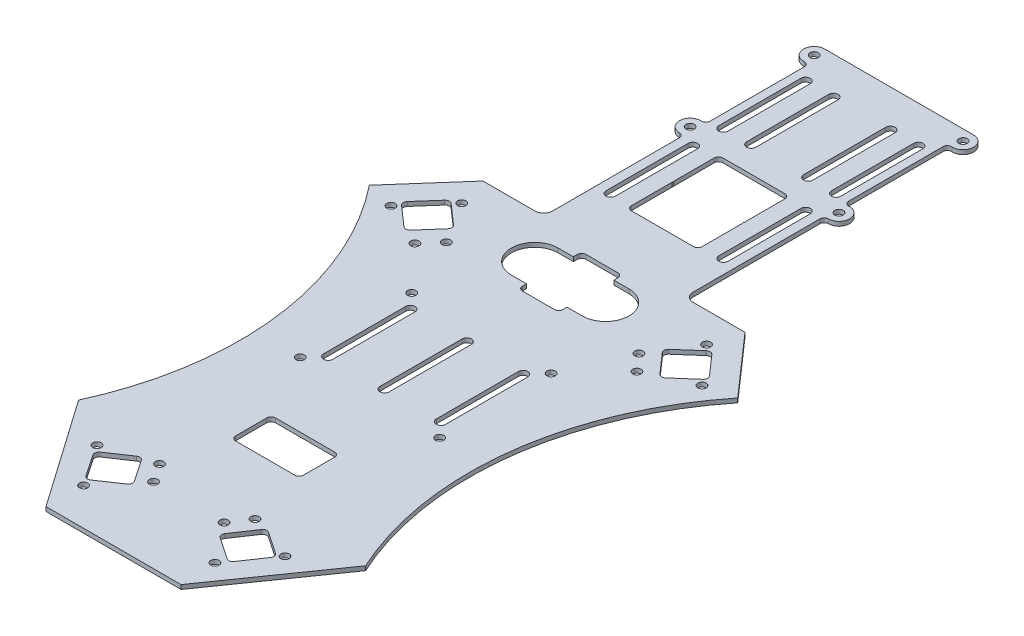
SolidWorks part; units mm, degrees
ref_plane "Front Plane" through (0, 0, 0) normal (0, 0, 1) x (1, 0, 0)
ref_plane "Top Plane" through (0, 0, 0) normal (0, 1, 0) x (1, 0, 0)
ref_plane "Right Plane" through (0, 0, 0) normal (1, 0, 0) x (0, 0, -1)
sketch "Sketch1" plane through (0, 0, 0) normal (0, 1, 0) x (1, 0, 0)
  line L0 (0, -163.8605) -> (0, 187.1526) construction
  line L1 (24.225, -100.314) -> (-24.225, -100.314)
  line L2 (-47, 79.196) -> (-66.075, 57.4987)
  line L3 (-51.475, -61.3813) -> (-24.225, -100.314)
  line L4 (-47, 79.196) -> (-28.38, 79.196)
  line L5 (-25.2, 82.376) -> (-25.2, 127.896)
  line L6 (26.7, 181.496) -> (-26.7, 181.496)
  line L7 (-24.85, 172.4076) -> (-24.85, 138.4845)
  line L8 (-20.22, 168.1277) -> (-20.22, 138.6677) construction
  line L9 (-18.54, 168.1277) -> (-18.54, 138.6677)
  line L10 (-21.9, 168.1277) -> (-21.9, 138.6677)
  line L11 (-10.22, 168.1277) -> (-10.22, 138.6677) construction
  line L12 (-8.54, 168.1277) -> (-8.54, 138.6677)
  line L13 (-11.9, 168.1277) -> (-11.9, 138.6677)
  line L14 (-20.22, 127.716) -> (-20.22, 98.256) construction
  line L15 (-18.54, 127.716) -> (-18.54, 98.256)
  line L16 (-21.9, 127.716) -> (-21.9, 98.256)
  line L17 (-20.22, 26.376) -> (-20.22, -3.084) construction
  line L18 (-18.54, 26.376) -> (-18.54, -3.084)
  line L19 (-21.9, 26.376) -> (-21.9, -3.084)
  line L20 (0, 26.376) -> (0, -3.084) construction
  line L21 (1.68, 26.376) -> (1.68, -3.084)
  line L22 (-1.68, 26.376) -> (-1.68, -3.084)
  line L23 (-54.1827, 59.2578) -> (-47.9366, 66.3626)
  line L24 (11.13, 129.396) -> (-11.13, 129.396)
  line L25 (12.7, 127.826) -> (12.7, 113.506)
  line L26 (11.13, 111.936) -> (-11.13, 111.936)
  line L27 (-12.7, 127.826) -> (-12.7, 113.506)
  line L28 (12.7, 129.396) -> (-12.7, 111.936) construction
  line L29 (12.7, 111.936) -> (-12.7, 129.396) construction
  line L30 (11.13, 114.036) -> (-11.13, 114.036)
  line L31 (12.7, 112.466) -> (12.7, 98.146)
  line L32 (11.13, 96.576) -> (-11.13, 96.576)
  line L33 (-12.7, 112.466) -> (-12.7, 98.146)
  line L34 (12.7, 114.036) -> (-12.7, 96.576) construction
  line L35 (12.7, 96.576) -> (-12.7, 114.036) construction
  line L36 (-54.0402, 57.0421) -> (-46.9354, 50.796)
  line L37 (-45.7209, 66.5051) -> (-38.6161, 60.2591)
  line L38 (-44.7197, 50.9385) -> (-38.4736, 58.0433)
  line L39 (-31.8561, -75.8408) -> (-26.6116, -83.5936)
  line L40 (-12.7, 71.876) -> (-7.265, 71.876)
  line L41 (-12.7, 55.076) -> (-7.265, 55.076)
  line L42 (7.265, 71.876) -> (12.7, 71.876)
  line L43 (5.695, 74.876) -> (-5.695, 74.876)
  line L44 (7.265, 73.306) -> (7.265, 71.876)
  line L45 (5.695, 52.076) -> (-5.695, 52.076)
  line L46 (-7.265, 73.306) -> (-7.265, 71.876)
  line L47 (7.265, 74.876) -> (6.9033, 74.3085) construction
  line L48 (7.265, 52.076) -> (6.9033, 52.6436) construction
  line L49 (7.265, 55.076) -> (7.265, 53.646)
  line L50 (-7.265, 55.076) -> (-7.265, 53.646)
  line L51 (-6.9033, 52.6436) -> (-7.265, 52.076) construction
  line L52 (7.265, 55.076) -> (12.7, 55.076)
  line L53 (-6.9033, 74.3085) -> (-7.265, 74.876) construction
  line L54 (-31.4354, -73.6607) -> (-23.6827, -68.4162)
  line L55 (-24.4315, -84.0143) -> (-16.6788, -78.7698)
  line L56 (-21.5026, -68.837) -> (-16.2581, -76.5897)
  line L57 (24.4315, -84.0143) -> (16.6788, -78.7698)
  line L58 (10.615, -31.604) -> (-10.615, -31.604)
  line L59 (12.185, -33.174) -> (12.185, -44.354)
  line L60 (10.615, -45.924) -> (-10.615, -45.924)
  line L61 (-12.185, -33.174) -> (-12.185, -44.354)
  line L62 (12.185, -31.604) -> (-12.185, -45.924) construction
  line L63 (12.185, -45.924) -> (-12.185, -31.604) construction
  line L64 (21.5026, -68.837) -> (16.2581, -76.5897)
  line L65 (31.4354, -73.6607) -> (23.6827, -68.4162)
  line L66 (31.8561, -75.8408) -> (26.6116, -83.5936)
  line L67 (51.475, -61.3813) -> (24.225, -100.314)
  line L68 (20.22, 26.376) -> (20.22, -3.084) construction
  line L69 (18.54, 26.376) -> (18.54, -3.084)
  line L70 (21.9, 26.376) -> (21.9, -3.084)
  line L71 (54.0402, 57.0421) -> (46.9354, 50.796)
  line L72 (44.7197, 50.9385) -> (38.4736, 58.0433)
  line L73 (45.7209, 66.5051) -> (38.6161, 60.2591)
  line L74 (54.1827, 59.2578) -> (47.9366, 66.3626)
  line L75 (47, 79.196) -> (66.075, 57.4987)
  line L76 (47, 79.196) -> (28.38, 79.196)
  line L77 (20.22, 127.716) -> (20.22, 98.256) construction
  line L78 (18.54, 127.716) -> (18.54, 98.256)
  line L79 (21.9, 127.716) -> (21.9, 98.256)
  line L80 (10.22, 168.1277) -> (10.22, 138.6677) construction
  line L81 (8.54, 168.1277) -> (8.54, 138.6677)
  line L82 (11.9, 168.1277) -> (11.9, 138.6677)
  line L83 (20.22, 168.1277) -> (20.22, 138.6677) construction
  line L84 (18.54, 168.1277) -> (18.54, 138.6677)
  line L85 (21.9, 168.1277) -> (21.9, 138.6677)
  line L86 (25.2, 82.376) -> (25.2, 127.896)
  line L87 (24.85, 172.4076) -> (24.85, 138.4845)
  arc A0 (-51.475, -61.3813) -> (-66.075, 57.4987) centre (-155.1713, -13.7801) ccw
  arc A1 (-26.7, 181.496) -> (-26.4491, 173.9043) centre (-26.7, 177.696) ccw
  arc A2 (-26.4491, 136.9877) -> (-26.7, 129.396) centre (-26.7, 133.196) ccw
  arc A3 (-25.2, 127.896) -> (-26.7, 129.396) centre (-26.7, 127.896) ccw
  arc A4 (-24.85, 138.4845) -> (-26.4491, 136.9877) centre (-26.35, 138.4845) cw
  arc A5 (-24.85, 172.4076) -> (-26.4491, 173.9043) centre (-26.35, 172.4076) ccw
  arc A6 (-25.2, 82.376) -> (-28.38, 79.196) centre (-28.38, 82.376) cw
  arc A7 (-18.54, 168.1277) -> (-21.9, 168.1277) centre (-20.22, 168.1277) ccw
  arc A8 (-21.9, 138.6677) -> (-18.54, 138.6677) centre (-20.22, 138.6677) ccw
  arc A9 (-8.54, 168.1277) -> (-11.9, 168.1277) centre (-10.22, 168.1277) ccw
  arc A10 (-11.9, 138.6677) -> (-8.54, 138.6677) centre (-10.22, 138.6677) ccw
  arc A11 (-18.54, 127.716) -> (-21.9, 127.716) centre (-20.22, 127.716) ccw
  arc A12 (-21.9, 98.256) -> (-18.54, 98.256) centre (-20.22, 98.256) ccw
  arc A13 (-18.54, 26.376) -> (-21.9, 26.376) centre (-20.22, 26.376) ccw
  arc A14 (-21.9, -3.084) -> (-18.54, -3.084) centre (-20.22, -3.084) ccw
  arc A15 (1.68, 26.376) -> (-1.68, 26.376) centre (0, 26.376) ccw
  arc A16 (-1.68, -3.084) -> (1.68, -3.084) centre (0, -3.084) ccw
  arc A17 (11.13, 96.576) -> (12.7, 98.146) centre (11.13, 98.146) ccw
  arc A18 (12.7, 112.466) -> (11.13, 114.036) centre (11.13, 112.466) ccw
  arc A19 (-12.7, 112.466) -> (-11.13, 114.036) centre (-11.13, 112.466) cw
  arc A20 (-11.13, 96.576) -> (-12.7, 98.146) centre (-11.13, 98.146) cw
  arc A21 (12.7, 113.506) -> (11.13, 111.936) centre (11.13, 113.506) cw
  arc A22 (-11.13, 111.936) -> (-12.7, 113.506) centre (-11.13, 113.506) cw
  arc A23 (-11.13, 129.396) -> (-12.7, 127.826) centre (-11.13, 127.826) ccw
  arc A24 (12.7, 127.826) -> (11.13, 129.396) centre (11.13, 127.826) ccw
  arc A25 (-46.9354, 50.796) -> (-44.7197, 50.9385) centre (-45.8988, 51.9751) ccw
  arc A26 (-54.0402, 57.0421) -> (-54.1827, 59.2578) centre (-53.0036, 58.2212) cw
  arc A27 (-38.4736, 58.0433) -> (-38.6161, 60.2591) centre (-39.6527, 59.0799) ccw
  arc A28 (-45.7209, 66.5051) -> (-47.9366, 66.3626) centre (-46.7575, 65.326) ccw
  arc A29 (-12.7, 71.876) -> (-12.7, 55.076) centre (-12.7, 63.476) ccw
  arc A30 (12.7, 55.076) -> (12.7, 71.876) centre (12.7, 63.476) ccw
  arc A31 (7.265, 53.646) -> (5.695, 52.076) centre (5.695, 53.646) cw
  arc A32 (7.265, 73.306) -> (5.695, 74.876) centre (5.695, 73.306) ccw
  arc A33 (-5.695, 74.876) -> (-7.265, 73.306) centre (-5.695, 73.306) ccw
  arc A34 (-7.265, 53.646) -> (-5.695, 52.076) centre (-5.695, 53.646) ccw
  arc A35 (-26.6116, -83.5936) -> (-24.4315, -84.0143) centre (-25.3112, -82.7139) ccw
  arc A36 (-16.6788, -78.7698) -> (-16.2581, -76.5897) centre (-17.5585, -77.4694) ccw
  arc A37 (-21.5026, -68.837) -> (-23.6827, -68.4162) centre (-22.803, -69.7166) ccw
  arc A38 (-31.8561, -75.8408) -> (-31.4354, -73.6607) centre (-30.5557, -74.9611) cw
  arc A39 (-12.185, -33.174) -> (-10.615, -31.604) centre (-10.615, -33.174) cw
  arc A40 (10.615, -31.604) -> (12.185, -33.174) centre (10.615, -33.174) cw
  arc A41 (12.185, -44.354) -> (10.615, -45.924) centre (10.615, -44.354) cw
  arc A42 (-10.615, -45.924) -> (-12.185, -44.354) centre (-10.615, -44.354) cw
  arc A43 (21.5026, -68.837) -> (23.6827, -68.4162) centre (22.803, -69.7166) cw
  arc A44 (46.9354, 50.796) -> (44.7197, 50.9385) centre (45.8988, 51.9751) cw
  arc A45 (45.7209, 66.5051) -> (47.9366, 66.3626) centre (46.7575, 65.326) cw
  arc A46 (54.0402, 57.0421) -> (54.1827, 59.2578) centre (53.0036, 58.2212) ccw
  arc A47 (38.4736, 58.0433) -> (38.6161, 60.2591) centre (39.6527, 59.0799) cw
  arc A48 (16.6788, -78.7698) -> (16.2581, -76.5897) centre (17.5585, -77.4694) cw
  arc A49 (26.6116, -83.5936) -> (24.4315, -84.0143) centre (25.3112, -82.7139) cw
  arc A50 (31.8561, -75.8408) -> (31.4354, -73.6607) centre (30.5557, -74.9611) ccw
  arc A51 (18.54, 26.376) -> (21.9, 26.376) centre (20.22, 26.376) cw
  arc A52 (21.9, -3.084) -> (18.54, -3.084) centre (20.22, -3.084) cw
  arc A53 (51.475, -61.3813) -> (66.075, 57.4987) centre (155.1713, -13.7801) cw
  arc A54 (25.2, 82.376) -> (28.38, 79.196) centre (28.38, 82.376) ccw
  arc A55 (18.54, 127.716) -> (21.9, 127.716) centre (20.22, 127.716) cw
  arc A56 (21.9, 98.256) -> (18.54, 98.256) centre (20.22, 98.256) cw
  arc A57 (8.54, 168.1277) -> (11.9, 168.1277) centre (10.22, 168.1277) cw
  arc A58 (11.9, 138.6677) -> (8.54, 138.6677) centre (10.22, 138.6677) cw
  arc A59 (18.54, 168.1277) -> (21.9, 168.1277) centre (20.22, 168.1277) cw
  arc A60 (21.9, 138.6677) -> (18.54, 138.6677) centre (20.22, 138.6677) cw
  arc A61 (25.2, 127.896) -> (26.7, 129.396) centre (26.7, 127.896) cw
  arc A62 (26.4491, 136.9877) -> (26.7, 129.396) centre (26.7, 133.196) cw
  arc A63 (24.85, 138.4845) -> (26.4491, 136.9877) centre (26.35, 138.4845) ccw
  arc A64 (24.85, 172.4076) -> (26.4491, 173.9043) centre (26.35, 172.4076) cw
  arc A65 (26.7, 181.496) -> (26.4491, 173.9043) centre (26.7, 177.696) cw
  point P23 (-24.85, 174.3768)
  point P26 (-25.2, 79.196)
  point P29 (-20.22, 153.3977)
  point P34 (-10.22, 153.3977)
  point P41 (-20.22, 136.9877)
  point P42 (0, 105.306)
  point P45 (-20.22, 112.986)
  point P50 (-20.22, 96.576)
  point P53 (-20.22, 129.396)
  point P58 (-20.22, 11.646)
  point P68 (0, 11.646)
  point P76 (-51.0597, 62.8102)
  point P77 (0, 120.666)
  point P118 (-46.9, 67.5418)
  point P121 (0, 63.476)
  point P126 (0, 63.476)
  point P149 (-29.2339, -79.7172)
  point P154 (-37.85, -80.8477)
  point P157 (-25.7319, -84.894)
  point P166 (0, -38.764)
  point P202 (0, -100.314)
  point P205 (20.22, 11.646)
  point P218 (20.22, 112.986)
  point P225 (10.22, 153.3977)
  point P232 (20.22, 153.3977)
  point P249 (0, 181.496)
  dimension "D1" = 48.45
  dimension "D4" = 114.1
  dimension "D8" = 7.6
  dimension "D9" = 7.6
  dimension "D11" = 49.7
  dimension "D16" = 1.5
  dimension "D17" = 3.18
  dimension "D18" = 1.68
  dimension "D25" = 1.57
  dimension "D29" = 1.57
  dimension "D30" = 8.4
  dimension "D34" = 1.57
  dimension "D35" = 1.57
  dimension "D40" = 1.57
  dimension "D45" = 1.57
  dimension "D2" = 27.25
  dimension "D3" = 14.6
  dimension "D5" = 118.88
  dimension "D6" = 28.89
  dimension "D7" = 21.8
  dimension "D10" = 26.7
  dimension "D12" = 44.5
  dimension "D13" = 6.31
  dimension "D14" = 102.3
  dimension "D15" = 281.81
  dimension "D19" = 29.46
  dimension "D20" = 10
  dimension "D21" = 20.22
  dimension "D22" = 155.12
  dimension "D23" = 25.4
  dimension "D24" = 12.5
  dimension "D26" = 12.6
  dimension "D27" = 7.77
  dimension "D28" = 21.7
  dimension "D31" = 7.32
  dimension "D32" = 14.53
  dimension "D33" = 22.8
  dimension "D36" = 12.5
  dimension "D37" = 12.5
  dimension "D38" = 7.77
  dimension "D39" = 15.42
  dimension "D41" = 7.77
  dimension "D42" = 24.37
  dimension "D43" = 14.32
  dimension "D44" = 213.1
  dimension "D46" = 14.32
extrude "Boss-Extrude1" add sketch "Sketch1" along normal blind 1.53 contours A65 L6 A1 A5 L7 A4 A2 A3 L5 A6 L4 L2 A0 L3 L1 L67 A53 L75 L76 A54 L86 A61 A62 A63 L87 A64 A50 L66 A49 L57 A48 L64 A43 L65 A34 L50 L41 A29 L40 L46 A33 L43 A32 L44 L42 A30 L52 L49 A31
sketch "Sketch2" plane through (0, 1.53, 0) normal (0, 1, 0) x (1, 0, 0)
  line L0 (-55.7847, 54.9808) -> (-43.9, 68.4994) construction
  line L1 (-51.0597, 62.8102) -> (-54.8635, 66.1543) construction
  line L2 (-54.1827, 59.2578) -> (-47.9366, 66.3626) construction
  line L3 (-39.8204, 47.6034) -> (-34.5383, 53.6116) construction
  line L4 (-41.5966, 54.4909) -> (-39.1657, 52.3538) construction
  line L5 (-44.7197, 50.9385) -> (-38.4736, 58.0433) construction
  line L6 (-25.005, 31.646) -> (-25.005, -8.354) construction
  line L7 (-21.9, 26.376) -> (-21.9, -3.084) construction
  line L8 (-12.185, -33.174) -> (-12.185, -44.354) construction
  line L9 (-21.9, 11.646) -> (-28.11, 11.646) construction
  line L10 (0, -116.2483) -> (0, 110.631) construction
  line L11 (-17.1237, -66.6957) -> (-12.6412, -73.322) construction
  line L12 (-29.2339, -79.7172) -> (-28.8942, -79.4874) construction
  line L13 (-31.8561, -75.8408) -> (-26.6116, -83.5936) construction
  line L14 (-18.8803, -72.7133) -> (-9.207, -66.1696) construction
  line L15 (-21.5026, -68.837) -> (-16.2581, -76.5897) construction
  line L16 (-51.475, -61.3813) -> (-24.225, -100.314) construction
  line L17 (-34.1468, -72.0886) -> (-24.0612, -86.9977) construction
  circle A0 centre (-26.7, 177.696) radius 1.5
  circle A1 centre (26.7, 177.696) radius 1.5
  circle A2 centre (-26.7, 133.196) radius 1.5
  circle A3 centre (26.7, 133.196) radius 1.5
  arc A4 (-26.7, 181.496) -> (-26.4491, 173.9043) centre (-26.7, 177.696) ccw construction
  arc A5 (26.4491, 173.9043) -> (26.7, 181.496) centre (26.7, 177.696) ccw construction
  arc A6 (-26.4491, 136.9877) -> (-26.7, 129.396) centre (-26.7, 133.196) ccw construction
  arc A7 (26.7, 129.396) -> (26.4491, 136.9877) centre (26.7, 133.196) ccw construction
  circle A8 centre (-39.8204, 47.6034) radius 1.5
  circle A9 centre (-34.5383, 53.6116) radius 1.5
  circle A10 centre (-55.7847, 54.9808) radius 1.5
  circle A11 centre (-43.9, 68.4994) radius 1.5
  arc A12 (-45.7209, 66.5051) -> (-47.9366, 66.3626) centre (-46.7575, 65.326) ccw construction
  circle A13 centre (-25.005, 31.646) radius 1.5
  circle A14 centre (-25.005, -8.354) radius 1.5
  circle A15 centre (-17.1237, -66.6957) radius 1.5
  circle A16 centre (-12.6412, -73.322) radius 1.5
  circle A17 centre (-34.1468, -72.0886) radius 1.5
  circle A18 centre (-24.0612, -86.9977) radius 1.5
  arc A19 (-26.6116, -83.5936) -> (-24.4315, -84.0143) centre (-25.3112, -82.7139) ccw construction
  circle A20 centre (34.0915, -72.8894) radius 1.5
  circle A21 centre (23.5364, -87.4699) radius 1.5
  circle A22 centre (12.6412, -73.322) radius 1.5
  circle A23 centre (17.1237, -66.6957) radius 1.5
  circle A24 centre (25.005, -8.354) radius 1.5
  circle A25 centre (25.005, 31.646) radius 1.5
  circle A26 centre (39.8204, 47.6034) radius 1.5
  circle A27 centre (34.5383, 53.6116) radius 1.5
  circle A28 centre (55.7847, 54.9808) radius 1.5
  circle A29 centre (43.9, 68.4994) radius 1.5
  point P32 (-46.8583, 66.8928)
  point P38 (-51.0597, 62.8102)
  point P43 (-37.1793, 50.6075)
  point P44 (-49.8424, 61.7401)
  point P52 (-34.5383, 53.6116)
  point P62 (-25.005, 11.646)
  point P73 (-29.064, -79.6023)
  point P75 (-14.8825, -70.0089)
  dimension "D1" = 3
  dimension "D2" = 3
  dimension "D3" = 12.32
  dimension "D4" = 8
  dimension "D6" = 18
  dimension "D7" = 12.82
  dimension "D9" = 18
  dimension "D11" = 1.25
  dimension "D5" = 3.1
  dimension "D8" = 40
  dimension "D10" = 8
  dimension "D12" = 12.67
  dimension "D13" = 7.77
extrude "Cut-Extrude1" cut sketch "Sketch2" against normal blind 1.53
